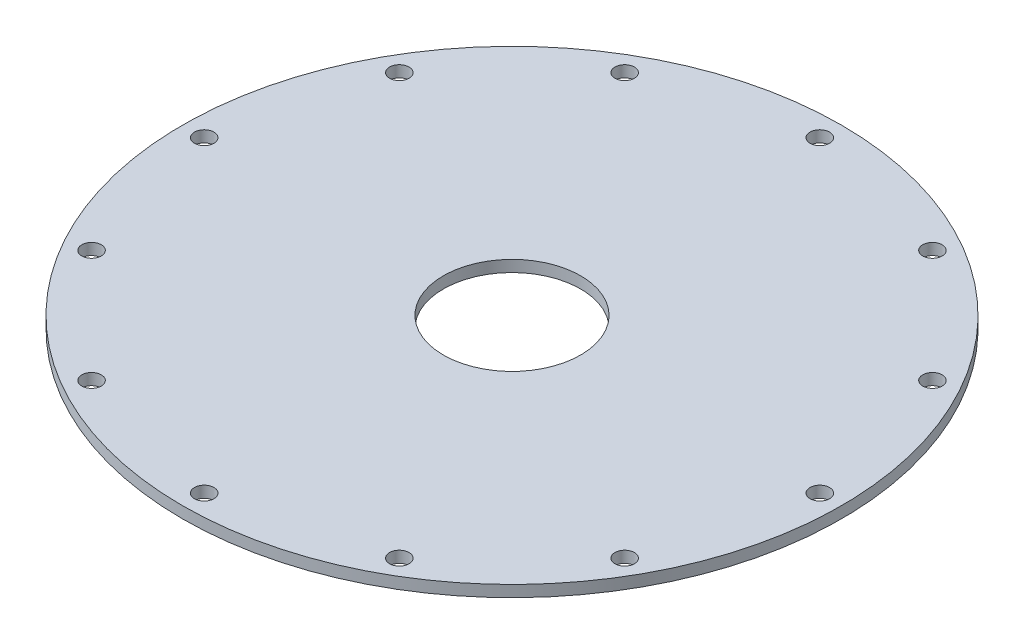
SolidWorks part; units mm, degrees
material "6063-T6"
ref_plane "Front Plane" through (0, 0, 0) normal (0, 0, 1) x (1, 0, 0)
ref_plane "Top Plane" through (0, 0, 0) normal (0, 1, 0) x (1, 0, 0)
ref_plane "Right Plane" through (0, 0, 0) normal (1, 0, 0) x (0, 0, -1)
ref_axis "Axis1" through (0, 55, 0) along (0, -1, 0)
sketch "Sketch1" plane through (0, 0, 0) normal (0, 0, 1) x (1, 0, 0)
  line L0 (-45.72, 0) -> (-9.525, 0)
  line L1 (0, 55) -> (0, -55) construction
  line L2 (-45.72, 0) -> (-45.72, 1.5875)
  line L3 (-45.72, 1.5875) -> (-9.525, 1.5875)
  line L4 (-45.72, 1.5875) -> (-9.525, 1.5875) construction
  line L5 (-9.525, 1.5875) -> (-9.525, 0)
  line L6 (-9.525, 0) -> (0, 0) construction
  line L7 (-45.72, 0) -> (-45.72, 1.5875) construction
  line L8 (-9.525, 1.5875) -> (-9.525, 0) construction
revolve "Revolve1" add sketch "Sketch1" angle 360 about axis through (0, 55, 0) along (0, -1, 0)
ref_plane "Hole Location Plane" through (0, 3.175, 0) normal (0, 1, 0) x (1, 0, 0)
sketch "Hole Location" plane through (0, 3.175, 0) normal (0, 1, 0) x (1, 0, 0)
  line L0 (0, 0) -> (-42.7006, 0) construction
  circle A0 centre (0, 0) radius 42.7006 construction
  dimension "D1" = 85.4012
hole_wizard "#36 (0.1065) Diameter Hole1" positions "Sketch4" profile "Sketch5" hole size "#36" standard "ANSI Inch" end condition through all
sketch "Sketch4" plane through (0, 1.5875, 0) normal (0, 1, 0) x (1, 0, 0)
  point P0 (-42.7006, 0)
sketch "Sketch5" plane through (-42.7006, 1.5875, 0) normal (1, 0, 0) x (0, 0, 1)
  line L0 (0, 0) -> (0, 1.5875)
  line L1 (0, 1.5875) -> (1.3525, 1.5875)
  line L2 (1.3525, 1.5875) -> (1.3525, 0)
  line L5 (1.3525, 0) -> (0, 0)
  line L11 (0, -6.35) -> (0, 107.95) construction
  dimension "Thru Hole Dia." = 2.7051
  dimension "Thru Hole Depth" = 1.5875
pattern_circular "CirPattern1" count 12 every 30 about axis through (0, 0, 0) along (0, 1, 0) of "#36 (0.1065) Diameter Hole1"
equation "\"D1@Hole Location\"=\"TANK DIAMETER@Cryo Tank.Assembly\"+\"GASKET SEAT THICKNESS@Cryo Tank.Assembly\"+\"LINER THICKNESS@Cryo Tank.Assembly\"+\"ALUMINUM LAP THICKNESS@Cryo Tank.Assembly\""
